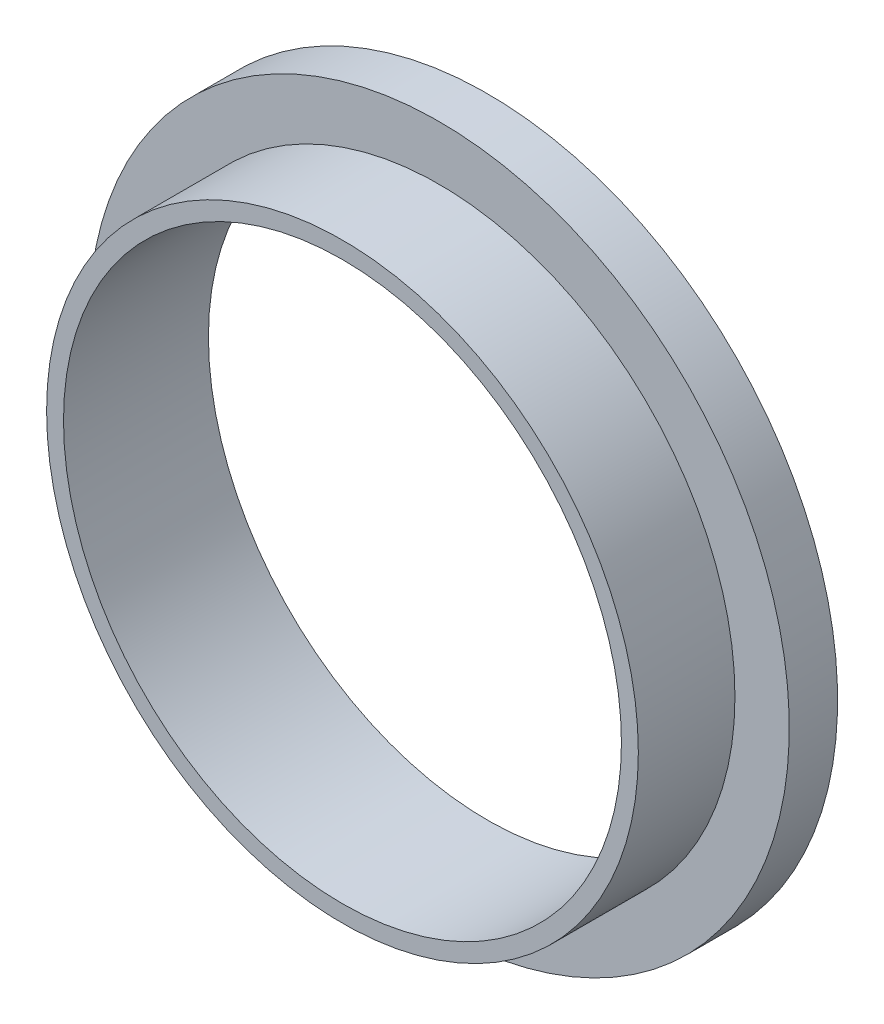
SolidWorks part; units mm, degrees
ref_plane "Front Plane" through (0, 0, 0) normal (0, 0, 1) x (1, 0, 0)
ref_plane "Top Plane" through (0, 0, 0) normal (0, 1, 0) x (1, 0, 0)
ref_plane "Right Plane" through (0, 0, 0) normal (1, 0, 0) x (0, 0, -1)
sketch "Croquis1" plane through (0, 0, 0) normal (0, 0, 1) x (1, 0, 0)
  circle A0 centre (0, 0) radius 12.25
  dimension "D1" = 24.5
extrude "Saliente-Extruir1" add sketch "Croquis1" along normal blind 4
sketch "Croquis2" plane through (0, 0, 0) normal (0, 0, -1) x (-1, 0, 0)
  circle A0 centre (0, 0) radius 14.5
  dimension "D1" = 29
extrude "Saliente-Extruir2" add sketch "Croquis2" along normal blind 2
sketch "Croquis3" plane through (0, 0, -2) normal (0, 0, -1) x (-1, 0, 0)
  circle A0 centre (0, 0) radius 11.55
  dimension "D1" = 23.1
extrude "Cortar-Extruir1" cut sketch "Croquis3" against normal blind 10
